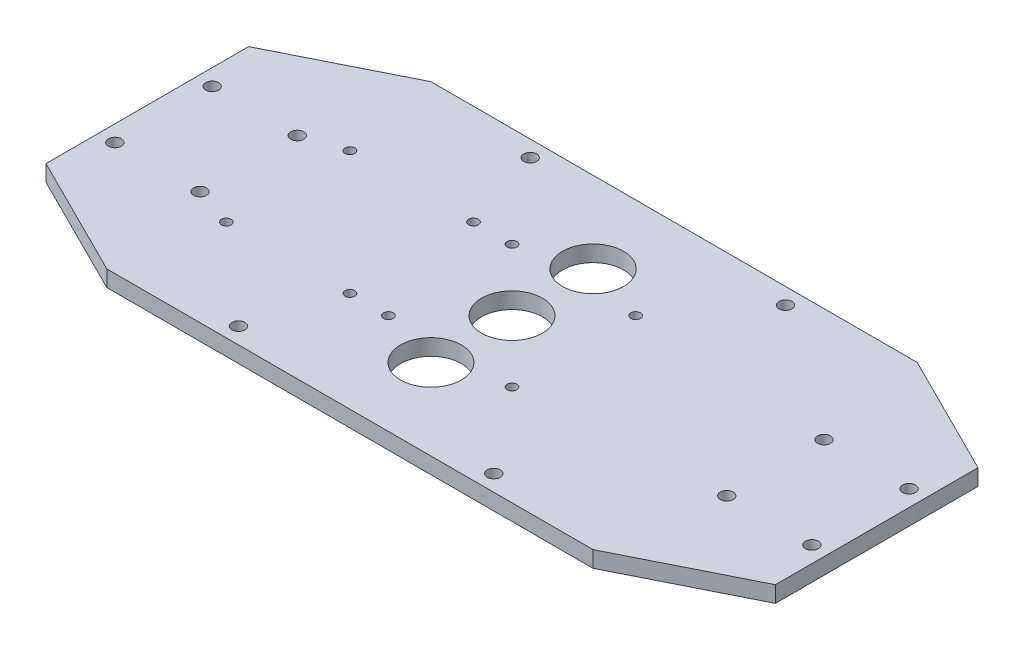
SolidWorks part; units mm, degrees
material "Pin"
ref_plane "Plan de face" through (0, 0, 0) normal (0, 0, 1) x (1, 0, 0)
ref_plane "Plan de dessus" through (0, 0, 0) normal (0, 1, 0) x (1, 0, 0)
ref_plane "Plan de droite" through (0, 0, 0) normal (1, 0, 0) x (0, 0, -1)
sketch "Esquisse1" plane through (0, 0, 0) normal (0, 1, 0) x (1, 0, 0)
  line L1 (0, 0) -> (180, 0)
  line L2 (0, 0) -> (0, 80)
  line L3 (0, 80) -> (180, 80)
  line L4 (180, 0) -> (180, 80)
  dimension "D1" = 180
  dimension "D2" = 80
extrude "Boss.-Extru.1" add sketch "Esquisse1" along normal blind 4
sketch "Esquisse2" plane through (0, 4, 0) normal (0, 1, 0) x (1, 0, 0)
  line L0 (0, 15) -> (30, 0)
  line L1 (0, 80) -> (0, 0) construction
  line L2 (0, 0) -> (180, 0) construction
  line L3 (30, 0) -> (0, 0)
  line L4 (0, 0) -> (0, 15)
  line L5 (30, 80) -> (0, 65)
  line L6 (180, 80) -> (0, 80) construction
  line L7 (0, 65) -> (0, 80)
  line L8 (0, 80) -> (30, 80)
  line L9 (150, 80) -> (180, 80)
  line L10 (180, 80) -> (180, 65)
  line L11 (180, 0) -> (180, 80) construction
  line L12 (180, 65) -> (150, 80)
  line L13 (180, 15) -> (150, 0)
  line L14 (150, 0) -> (180, 0)
  line L15 (180, 0) -> (180, 15)
  dimension "D1" = 30
  dimension "D2" = 15
  dimension "D3" = 30
  dimension "D4" = 15
  dimension "D5" = 15
  dimension "D6" = 30
  dimension "D7" = 30
  dimension "D8" = 15
extrude "Enlèv. mat.-Extru.1" cut sketch "Esquisse2" against normal blind 4
hole_wizard "Dégagement M22" positions "Esquisse9" profile "Esquisse10" size "M2" standard "ISO" slot yes end condition through all
sketch "Esquisse9" plane through (0, 4, 0) normal (0, 1, 0) x (1, 0, 0)
  point P0 (74.75, 55.25)
  point P3 (105.25, 55.25)
  point P6 (105.25, 24.75)
  point P9 (74.75, 24.75)
sketch "Esquisse10" plane through (74.75, 4, -55.25) normal (1, 0, 0) x (0, 0, 1)
  line L0 (0, 0) -> (0, 4)
  line L1 (0, 4) -> (1.2, 4)
  line L2 (1.2, 4) -> (1.2, 0)
  line L5 (1.2, 0) -> (0, 0)
  line L11 (0, -6.35) -> (0, 107.95) construction
  dimension "Diamètre du perçage jusqu'au prochain" = 2.4
  dimension "Profondeur du perçage jusqu'au prochain" = 4
hole_wizard "Dégagement M23" positions "Esquisse11" profile "Esquisse12" size "M2" standard "ISO" slot yes end condition through all
sketch "Esquisse11" plane through (0, 4, 0) normal (0, 1, 0) x (1, 0, 0)
  point P0 (34.75, 24.75)
  point P3 (65.25, 24.75)
  point P6 (65.25, 55.25)
  point P9 (34.75, 55.25)
sketch "Esquisse12" plane through (34.75, 4, -24.75) normal (1, 0, 0) x (0, 0, 1)
  line L0 (0, 0) -> (0, 4)
  line L1 (0, 4) -> (1.2, 4)
  line L2 (1.2, 4) -> (1.2, 0)
  line L5 (1.2, 0) -> (0, 0)
  line L11 (0, -6.35) -> (0, 107.95) construction
  dimension "Diamètre du perçage jusqu'au prochain" = 2.4
  dimension "Profondeur du perçage jusqu'au prochain" = 4
hole_wizard "Dégagement M31" positions "Esquisse15" profile "Esquisse16" hole size "M3" standard "ISO" end condition up to next
sketch "Esquisse15" plane through (0, 4, 0) normal (0, 1, 0) x (1, 0, 0)
  point P0 (4, 52)
  point P2 (4, 28)
  point P4 (25, 28)
  point P6 (25, 52)
  point P8 (58.5, 76)
  point P10 (58.5, 4)
  point P12 (121.5, 4)
  point P14 (121.5, 76)
  point P16 (155, 52)
  point P18 (176, 52)
  point P20 (176, 28)
  point P22 (155, 28)
sketch "Esquisse16" plane through (4, 4, -52) normal (1, 0, 0) x (0, 0, 1)
  line L0 (0, 0) -> (0, 4)
  line L1 (0, 4) -> (1.6, 4)
  line L2 (1.6, 4) -> (1.6, 0)
  line L5 (1.6, 0) -> (0, 0)
  line L11 (0, -6.35) -> (0, 107.95) construction
  dimension "Diamètre du perçage jusqu'au prochain" = 3.2
  dimension "Profondeur du perçage jusqu'au prochain" = 4
sketch "Esquisse17" plane through (0, 4, 0) normal (0, 1, 0) x (1, 0, 0)
  circle A0 centre (90, 60) radius 7.534
  circle A1 centre (90, 40) radius 7.5
  circle A2 centre (90, 20) radius 7.5
extrude "Enlèv. mat.-Extru.2" cut sketch "Esquisse17" against normal blind 10
equation "\"D8@Esquisse2\"=\"D2@Esquisse2\""
equation "\"D5@Esquisse2\"=\"D2@Esquisse2\""
equation "\"D4@Esquisse2\"=\"D2@Esquisse2\""
